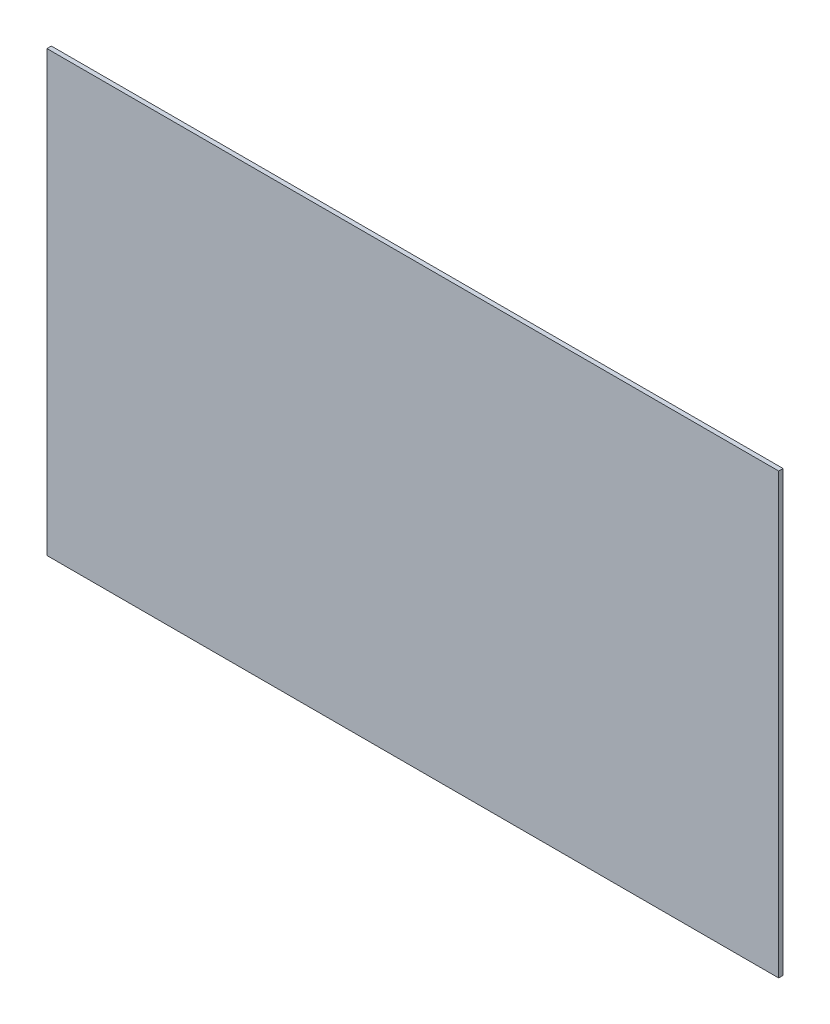
SolidWorks part; units mm, degrees
ref_plane "Ön Düzlem" through (0, 0, 0) normal (0, 0, 1) x (1, 0, 0)
ref_plane "Üst Düzlem" through (0, 0, 0) normal (0, 1, 0) x (1, 0, 0)
ref_plane "Sağ Düzlem" through (0, 0, 0) normal (1, 0, 0) x (0, 0, -1)
sketch "Çizim1" plane through (0, 0, 0) normal (0, 0, 1) x (1, 0, 0)
  line L1 (0, 0) -> (500, 0)
  line L2 (0, 0) -> (0, -300)
  line L3 (0, -300) -> (500, -300)
  line L4 (500, 0) -> (500, -300)
  dimension "D1" = 500
  dimension "D2" = 300
extrude "Yükseklik-Ekstrüzyon1" add sketch "Çizim1" along normal blind 3 contours L1 L4 L3 L2
